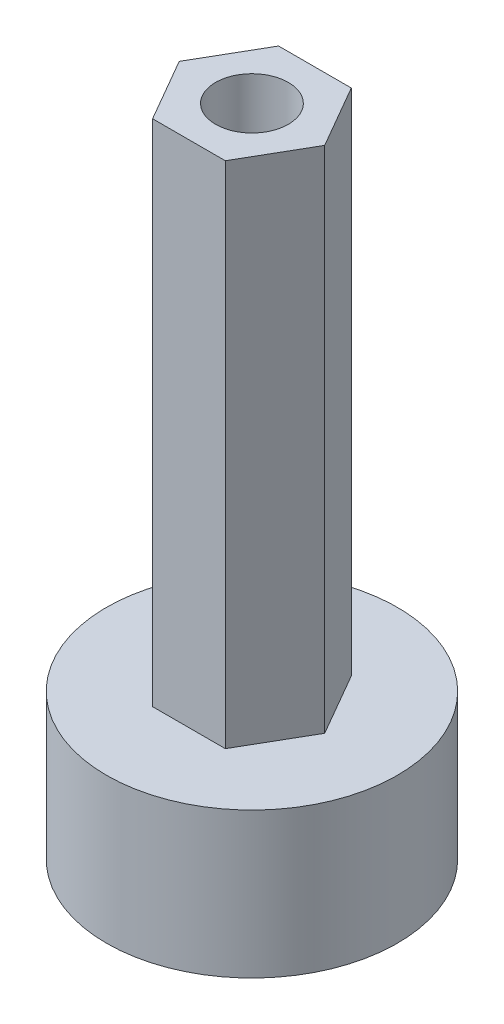
SolidWorks part; units mm, degrees
ref_plane "Front" through (0, 0, 0) normal (0, 0, 1) x (1, 0, 0)
ref_plane "Top" through (0, 0, 0) normal (0, 1, 0) x (1, 0, 0)
ref_plane "Right" through (0, 0, 0) normal (1, 0, 0) x (0, 0, -1)
sketch "Sketch2" plane through (0, 0, 0) normal (0, 0, 1) x (1, 0, 0)
  line L0 (0, 41.227) -> (0, -41.227) construction
  line L2 (6.35, 0) -> (6.35, 6.35)
  line L3 (6.35, 6.35) -> (3.175, 6.35)
  line L4 (3.175, 6.35) -> (3.175, 28.575)
  line L5 (3.175, 28.575) -> (1.5875, 28.575)
  line L6 (1.5875, 28.575) -> (1.5875, 3.175)
  line L7 (6.35, 0) -> (3.175, 0)
  line L8 (3.175, 0) -> (3.175, 3.175)
  line L9 (3.175, 3.175) -> (1.5875, 3.175)
  dimension "D1" = 3.175
  dimension "D2" = 6.35
  dimension "D3" = 6.35
  dimension "D4" = 12.7
  dimension "D5" = 3.175
  dimension "D6" = 3.175
  dimension "D7" = 22.225
revolve "Revolve1" add sketch "Sketch2" angle 360 about L0
sketch "Sketch3" plane through (0, 28.575, 0) normal (0, 1, 0) x (1, 0, 0)
  line L1 (-1.5875, 2.7496) -> (-3.175, 0)
  line L2 (-3.175, 0) -> (-1.5875, -2.7496)
  line L3 (-1.5875, -2.7496) -> (1.5875, -2.7496)
  line L4 (1.5875, -2.7496) -> (3.175, 0)
  line L5 (3.175, 0) -> (1.5875, 2.7496)
  line L6 (1.5875, 2.7496) -> (-1.5875, 2.7496)
  circle A0 centre (0, 0) radius 3.175
  circle A1 centre (0, 0) radius 3.175 construction
  circle M8 centre (0, 0) radius 3.175
extrude "Cut-Extrude3" cut sketch "Sketch3" against normal up to surface (22.225 mm away) contours L1 M8 | L6 M8 | L5 M8 | L4 M8 | L3 M8 | L2 M8 up to face at (0, 6.35, 3.175)
sketch "Sketch4" plane through (0, 0, 0) normal (0, -1, 0) x (1, 0, 0)
  line L1 (1.8331, 3.175) -> (-1.8331, 3.175)
  line L2 (-1.8331, 3.175) -> (-3.6662, 0)
  line L3 (-3.6662, 0) -> (-1.8331, -3.175)
  line L4 (-1.8331, -3.175) -> (1.8331, -3.175)
  line L5 (1.8331, -3.175) -> (3.6662, 0)
  line L6 (3.6662, 0) -> (1.8331, 3.175)
  circle A0 centre (0, 0) radius 3.175
  circle A1 centre (0, 0) radius 3.175 construction
  circle M9 centre (0, 0) radius 3.175
extrude "Cut-Extrude4" cut sketch "Sketch4" against normal up to surface (3.175 mm away) contours L1 L2 M9 | L6 L1 M9 | L5 L6 M9 | L4 L5 M9 | L3 L4 M9 | L2 L3 M9 | A0 up to face at (0, 3.175, 3.175)
